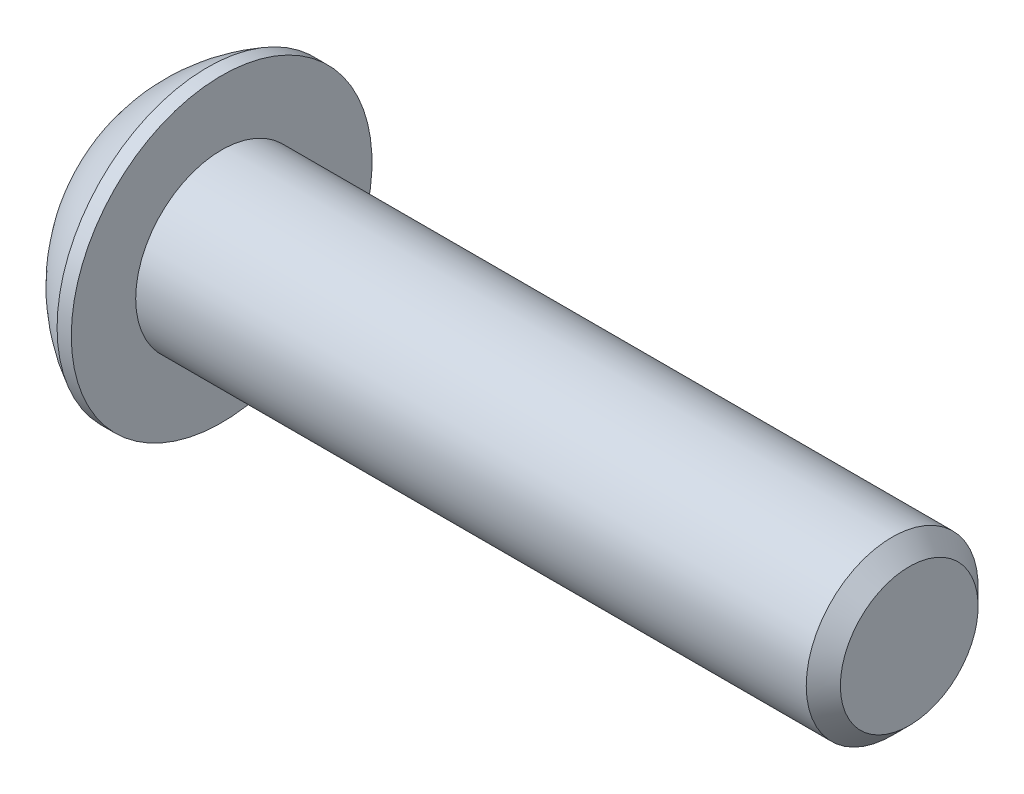
SolidWorks part; units mm, degrees
ref_plane "Plane1" through (0, 0, 0) normal (0, 0, 1) x (1, 0, 0)
ref_plane "Plane2" through (0, 0, 0) normal (0, 1, 0) x (1, 0, 0)
ref_plane "Plane3" through (0, 0, 0) normal (1, 0, 0) x (0, 0, -1)
sketch "BodySke" plane through (0, 0, 0) normal (0, 0, 1) x (1, 0, 0)
  line L0 (42.9768, 0) -> (42.9768, 3.8163)
  line L1 (42.0306, 4.7625) -> (4.8768, 4.7625)
  line L2 (4.8768, 4.7625) -> (4.8768, 8.3312)
  line L3 (4.8768, 8.3312) -> (4.0894, 8.3312)
  line L4 (0, 0) -> (101.6, 0) construction
  line L5 (4.8768, -8.3312) -> (4.0894, -8.3312) construction
  line L6 (55.6768, -4.7625) -> (4.8768, -4.7625) construction
  line L7 (42.9768, 0) -> (0, 0)
  line L8 (0, 4.1656) -> (0, -4.1656) construction
  line L9 (0, 0) -> (0, 4.1656)
  line L10 (42.9768, 3.8163) -> (42.0306, 4.7625)
  line L11 (42.9768, -3.8163) -> (42.0306, -4.7625) construction
  line L12 (6.4643, 9.525) -> (6.4643, -4.7625) construction
  line L13 (28.575, 9.525) -> (28.575, -4.7625) construction
  arc A1 (0, 4.1656) -> (4.0894, 8.3312) centre (8.4095, 0) cw
  dimension "D1" = 8.3312
  dimension "Diameter" = 9.525
  dimension "Length" = 38.1
  dimension "Head_dia" = 16.6624
  dimension "Head_ht" = 4.8768
  dimension "Head_side_ht" = 0.7874
  dimension "Minor_dia" = 7.6327
  dimension "Body_ch_ang" = 45
  dimension "Advance" = 1.5875
  dimension "Thread_nom" = 14.4018
revolve "BaseBody" add sketch "BodySke" angle 360 about L4
cosmetic thread "ThreadCosmetic" [suppressed] parameters "Thread_length"=14.4018, "Thread_minor"=7.6327
sketch "Sketch2" plane through (0, 0, 0) normal (0, 0, 1) x (1, 0, 0)
  line L0 (0, 2.7813) -> (3.0988, 2.7813)
  line L1 (3.0988, 2.7813) -> (4.7046, 0)
  line L3 (4.7046, 0) -> (0, 0)
  line L4 (0, 0) -> (0, 2.7813)
  line L5 (0, -2.7813) -> (3.0988, -2.7813) construction
  line L6 (0, 0) -> (47.625, 0) construction
  dimension "D2" = 60
  dimension "PreBroach_depth" = 3.0988
  dimension "PreBroach_dia" = 5.5626
revolve "PreBroach" cut sketch "Sketch2" angle 360 about L6
sketch "Sketch3" plane through (0, 0, 0) normal (1, 0, 0) x (0, 0, -1)
  line L0 (-2.7813, -1.6058) -> (-2.7813, 1.6058)
  line L1 (-2.7813, 1.6058) -> (0, 3.2116)
  line L2 (0, 3.2116) -> (2.7813, 1.6058)
  line L3 (2.7813, 1.6058) -> (2.7813, -1.6058)
  line L4 (2.7813, -1.6058) -> (0, -3.2116)
  line L5 (0, -3.2116) -> (-2.7813, -1.6058)
  dimension "D1" = 2.7813
  dimension "D2" = 2.7813
  dimension "D3" = 5.5626
  dimension "Hex_size" = 5.5626
extrude "Hex" cut sketch "Sketch3" along normal blind 3.0988
sketch "Sketch4" plane through (0, 9.525, 0) normal (1, 0, 0) x (0, 0, -1)
  line L0 (0, -9.525) -> (3.2512, -9.525)
  line L1 (0, -9.525) -> (6.1484, -5.9752) construction
  line L2 (0, -9.525) -> (1.6256, -6.7094)
  line L3 (2.7204, -8.8343) -> (3.1182, -8.6046)
  line L4 (1.9584, -7.5144) -> (2.3562, -7.2848)
  arc A0 (2.7204, -8.8343) -> (1.9584, -7.5144) centre (0, -9.525) ccw
  arc A1 (3.2512, -9.525) -> (3.1182, -8.6046) centre (0, -9.525) ccw
  arc A2 (1.6256, -6.7094) -> (2.3562, -7.2848) centre (0, -9.525) cw
  dimension "D1" = 30
  dimension "Spline_n_dim" = 5.6134
  dimension "Spline_m_dim" = 6.5024
  dimension "D2" = 60
  dimension "D3" = 0.762
  dimension "Spline_p_dim" = 1.524
extrude "Spline" [suppressed] cut sketch "Sketch4" along normal blind 3.0988
pattern_circular "CirPattern1" [suppressed] count 6 every 60 about axis through (0, 0, 0) along (1, 0, 0)
sketch "ThdSchSke" plane through (0, 0, 0) normal (0, 0, 1) x (1, 0, 0)
  line L0 (28.575, -3.8163) -> (27.9125, -4.7625)
  line L1 (28.575, -3.8163) -> (29.2375, -4.7625)
  line L2 (29.2375, -4.7625) -> (29.2375, -5.9531)
  line L3 (-3.175, 0) -> (5.1513, 0) construction
  line L5 (29.2375, -5.9531) -> (27.9125, -5.9531)
  line L6 (27.9125, -5.9531) -> (27.9125, -4.7625)
  dimension "Thread_minor" = 7.6327
  dimension "Diameter" = 9.525
  dimension "Start" = 28.575
  dimension "SideAngle" = 55
  dimension "VeeAngle" = 70
  dimension "Overcut" = 11.9063
revolve "ThreadSchematic" [suppressed] cut sketch "ThdSchSke" angle 360 about L3
pattern_linear "ThdSchPat" [suppressed]
equation "\"D1@BodySke\" = \"Head_dia@BodySke\" * .5"
equation "\"Thread_minor@ThreadCosmetic\" = \"Minor_dia@BodySke\""
equation "\"D1@Sketch3\" = \"Hex_size@Sketch3\" / 2"
equation "\"D2@Sketch3\" = \"D1@Sketch3\""
equation "\"D3@Sketch3\" = \"Hex_size@Sketch3\""
equation "\"D3@Sketch4\" = \"Spline_p_dim@Sketch4\" / 2"
equation "\"D1@Sketch4\" = \"D2@Sketch4\" / 2"
equation "\"Thread_length@ThreadCosmetic\" = ((sgn( (\"Length@BodySke\" - \"Advance@BodySke\" ) - \"Thread_nom@BodySke\" )-1)*( (\"Length@BodySke\" - \"Advance@BodySke\" ) - \"Thread_nom@BodySke\" ))/-2+ \"Thread_nom@BodySke\""
equation "\"Thread_minor@ThdSchSke\" = \"Minor_dia@BodySke\""
equation "\"Diameter@ThdSchSke\" = \"Diameter@BodySke\""
equation "\"Overcut@ThdSchSke\" = \"Diameter@BodySke\" * 1.25"
equation "\"Start@ThdSchSke\" = \"Head_ht@BodySke\" + \"Length@BodySke\" - \"Thread_length@ThreadCosmetic\"  '---Non-countersunk---"
equation "\"Num_threads@ThdSchPat\" = int( \"Thread_length@ThreadCosmetic\" / \"Advance@BodySke\" + 0.999 )  + 1"
equation "\"Advance@ThdSchPat\" = \"Thread_length@ThreadCosmetic\" /  (\"Num_threads@ThdSchPat\" - 1) 'relax it"
equation "\"Num_threads@ThdSchPat\" = \"Num_threads@ThdSchPat\" - sgn( \"Num_threads@ThdSchPat\" - 1) '---chamfered tips only---"
